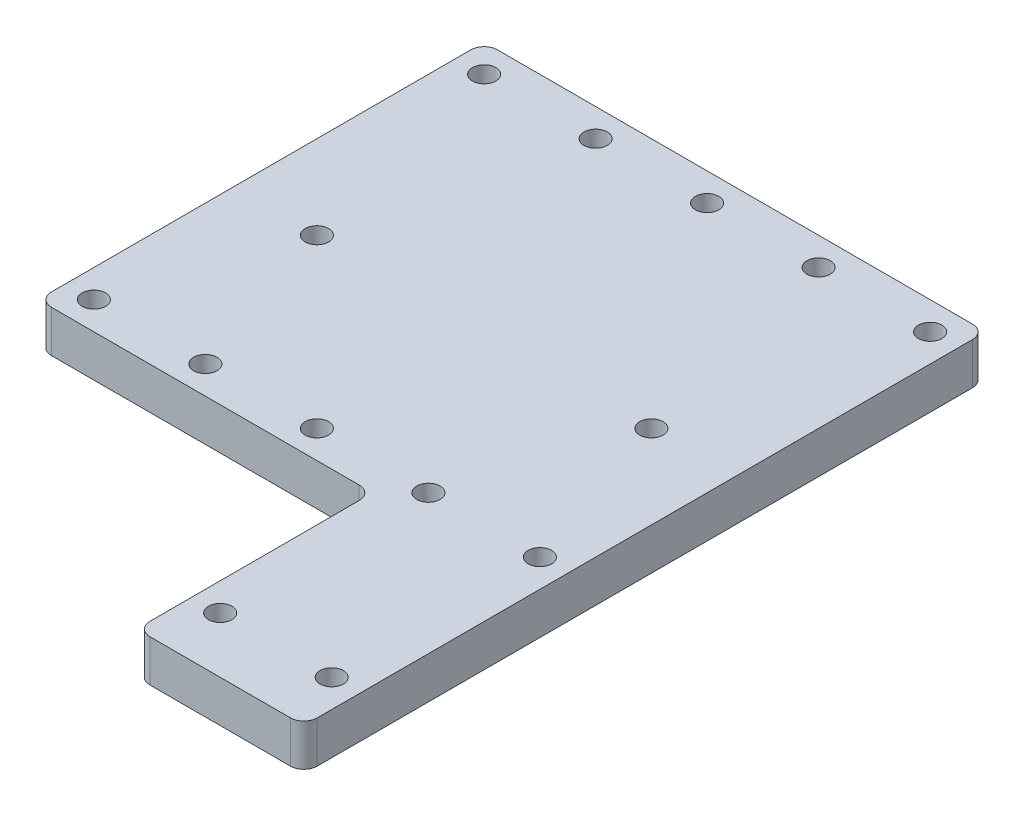
SolidWorks part; units mm, degrees
ref_plane "Front Plane" through (0, 0, 0) normal (0, 0, 1) x (1, 0, 0)
ref_plane "Top Plane" through (0, 0, 0) normal (0, 1, 0) x (1, 0, 0)
ref_plane "Right Plane" through (0, 0, 0) normal (1, 0, 0) x (0, 0, -1)
sketch "Sketch1" plane through (0, 0, 0) normal (0, 1, 0) x (1, 0, 0)
  line L1 (-19.05, 78.4162) -> (19.05, 78.4162)
  line L2 (-19.05, 78.4162) -> (-19.05, -78.4161)
  line L3 (-19.05, -78.4161) -> (19.05, -78.4161)
  line L4 (19.05, 78.4162) -> (19.05, -78.4161)
  line L5 (-19.05, 78.4162) -> (19.05, -78.4161) construction
  line L6 (-19.05, -78.4161) -> (19.05, 78.4162) construction
  point P0 (0, 0)
  dimension "D1" = 156.8323
extrude "Boss-Extrude1" add sketch "Sketch1" along normal blind 9.525
fillet "Fillet1" radius 3.048 2 edges at (19.05, 4.7625, 78.4161) (-19.05, 4.7625, 78.4161)
fillet "Fillet2" radius 3.048 1 edges at (-19.05, 4.7625, -78.4162)
fillet "Fillet3" radius 3.048 1 edges at (19.05, 4.7625, -78.4162)
sketch "Sketch2" plane through (0, 9.525, 0) normal (0, 1, 0) x (1, 0, 0)
  line L0 (19.05, 75.3682) -> (19.05, 79.9734)
  line L1 (10.6047, 78.4162) -> (19.05, 78.4162)
  line L2 (16.002, 78.4162) -> (-16.002, 78.4162) construction
  line L3 (19.05, 78.4162) -> (19.05, 72.0662)
  line L4 (19.05, -75.3681) -> (19.05, 75.3682) construction
  line L5 (19.05, 72.0662) -> (12.7, 72.0662)
  line L6 (12.7, 72.0662) -> (-12.7, 72.0662)
  line L7 (-6.5673, -78.4161) -> (-20.2495, -78.4161)
  line L8 (-16.002, -78.4161) -> (16.002, -78.4161) construction
  line L9 (-19.05, -74.1432) -> (-19.05, -78.4161)
  line L10 (-19.05, 75.3682) -> (-19.05, -75.3681) construction
  line L11 (-19.05, -78.4161) -> (-19.05, -67.4306)
  line L12 (-19.05, -67.4306) -> (-12.7, -67.4306)
  line L13 (-12.7, -67.4306) -> (12.7, -67.4306)
  line L14 (-12.7, 72.0662) -> (-12.7, -16.8338)
  line L15 (12.7, 72.0662) -> (12.7, -16.8338)
  line L16 (-12.7, -67.4306) -> (-12.7, -64.2557)
  line L17 (-12.7, -64.2557) -> (12.7, -64.2557)
  circle A0 centre (-12.7, 72.0662) radius 2.667
  circle A1 centre (12.7, 72.0662) radius 2.667
  circle A4 centre (-12.7, -16.8338) radius 2.667
  circle A5 centre (12.7, -16.8338) radius 2.667
  circle A6 centre (-12.7, -64.2557) radius 2.667
  circle A7 centre (12.7, -64.2557) radius 2.667
  dimension "D1" = 6.35
  dimension "D4" = 10.9855
  dimension "D5" = 88.9
  dimension "D2" = 6.35
  dimension "D3" = 25.4
  dimension "D6" = 88.9
extrude "Cut-Extrude1" cut sketch "Sketch2" against normal blind 25.4
sketch "Sketch3" plane through (0, 9.525, 0) normal (0, 1, 0) x (1, 0, 0)
  line L0 (-12.7, -64.2557) -> (-12.7, -76.9557)
  line L1 (-19.05, -73.9077) -> (-19.05, -76.9557)
  line L2 (-19.05, 75.3682) -> (-19.05, -75.3681) construction
  line L3 (-19.05, -76.9557) -> (-12.7, -76.9557)
  line L4 (-19.05, -73.9077) -> (-16.002, -76.9557)
  line L5 (-16.002, -76.9557) -> (-16.002, -73.9077)
  line L6 (-12.7, -76.9557) -> (19.05, -76.9557)
  line L7 (19.05, -76.9557) -> (19.05, -73.9077)
  line L8 (19.05, -75.3681) -> (19.05, 75.3682) construction
  line L9 (19.05, -73.9077) -> (16.002, -76.9557)
  line L10 (16.002, -76.9557) -> (16.002, -73.9077)
  line L11 (19.05, -76.9557) -> (19.05, -80.3022)
  line L12 (19.05, -80.3022) -> (16.002, -78.4161)
  line L13 (16.002, -78.4161) -> (-16.002, -78.4161)
  line L14 (-16.002, -78.4161) -> (-19.05, -79.3592)
  line L15 (-19.05, -79.3592) -> (-19.05, -76.9557)
  arc A1 (-19.05, -73.9077) -> (-16.002, -76.9557) centre (-16.002, -73.9077) ccw
  arc A2 (19.05, -73.9077) -> (16.002, -76.9556) centre (16.002, -73.9077) cw
  line M11 (19.05, -75.3681) -> (19.05, 75.3682)
  line M15 (-19.05, 75.3682) -> (-19.05, -75.3681)
  arc M16 (-19.05, -75.3681) -> (-16.002, -78.4161) centre (-16.002, -75.3681) ccw
  line M17 (-16.002, -78.4161) -> (16.002, -78.4161)
  arc M18 (16.002, -78.4161) -> (19.05, -75.3681) centre (16.002, -75.3681) ccw
extrude "Cut-Extrude2" cut sketch "Sketch3" against normal blind 29.718 contours A1 L3 M15 M16 | L6 L3 M16 M17 M18 | A2 L6 M11 M18
sketch "Sketch4" plane through (0, 0, 0) normal (0, -1, 0) x (1, 0, 0)
  line L0 (-88.9, -72.0662) -> (-95.25, -72.0662)
  line L1 (-88.9, -72.0662) -> (-88.9, -78.4162)
  line L2 (-88.9, -78.4162) -> (-16.002, -78.4162)
  line L3 (-88.9, -78.4162) -> (-95.25, -78.4162)
  line L4 (-95.25, -78.4162) -> (-95.25, -72.0662)
  line L5 (-12.7, 16.8338) -> (-12.7, 23.1839)
  line L6 (-12.7, 23.1839) -> (-19.05, 23.1839)
  line L7 (-19.05, -75.3682) -> (-19.05, 73.9077) construction
  line L8 (-19.05, 23.1839) -> (-95.25, 23.1839)
  line L9 (-95.25, 23.1839) -> (-95.25, -72.0662)
  line L10 (-19.05, 23.1839) -> (-19.05, -75.3682)
  line L11 (-95.25, -78.4162) -> (-95.25, -75.3681)
  line L12 (-95.25, -75.3681) -> (-92.202, -75.3682)
  line L13 (-95.25, 23.1839) -> (-95.25, 20.1359)
  line L14 (-95.25, 20.1359) -> (-92.202, 20.1359)
  line L15 (-19.05, 23.1839) -> (-22.098, 23.1839)
  line L16 (-22.098, 23.1839) -> (-22.098, 26.2319)
  line L17 (-19.05, 26.2319) -> (-19.05, 23.1839)
  circle A0 centre (-12.7, -72.0662) radius 2.667
  circle A1 centre (-12.7, 16.8338) radius 2.667
  circle A4 centre (-38.1, 16.8338) radius 2.667
  circle A5 centre (-38.1, -72.0662) radius 2.667
  circle A7 centre (-63.5, 16.8338) radius 2.667
  circle A8 centre (-63.5, -72.0662) radius 2.667
  circle A10 centre (-88.9, 16.8338) radius 2.667
  circle A11 centre (-88.9, -72.0662) radius 2.667
  arc A13 (-19.05, -75.3682) -> (-16.002, -78.4162) centre (-16.002, -75.3682) ccw construction
  arc A14 (-19.05, -75.3682) -> (-16.002, -78.4162) centre (-16.002, -75.3682) ccw
  arc A15 (-95.25, -75.3681) -> (-92.202, -78.4162) centre (-92.202, -75.3682) ccw
  arc A16 (-95.25, 20.1359) -> (-92.202, 23.1839) centre (-92.202, 20.1359) cw
  arc A17 (-22.098, 23.1839) -> (-19.05, 26.2319) centre (-22.098, 26.2319) ccw
  dimension "D1" = 4
extrude "Boss-Extrude2" add sketch "Sketch4" against normal up to surface (9.525 mm away)
sketch "Sketch5" plane through (0, 0, 0) normal (0, -1, 0) x (1, 0, 0)
  circle A0 centre (-63.5, 16.8338) radius 2.667
  circle A1 centre (12.7, 16.8338) radius 2.667
  circle A2 centre (0, 16.8338) radius 2.667
  circle A3 centre (-76.2, 16.8338) radius 2.667
  circle A4 centre (0, -21.2662) radius 2.667
  circle A5 centre (-76.2, -21.2662) radius 2.667
  circle A6 centre (12.7, -21.2662) radius 2.667
  circle A7 centre (-63.5, -21.2662) radius 2.667
  dimension "D1" = 2
  dimension "D2" = 2
extrude "Cut-Extrude3" cut sketch "Sketch5" against normal up to surface (9.525 mm away) contours A4 | A5 up to face at (-31.75, 9.525, 7.2411)
